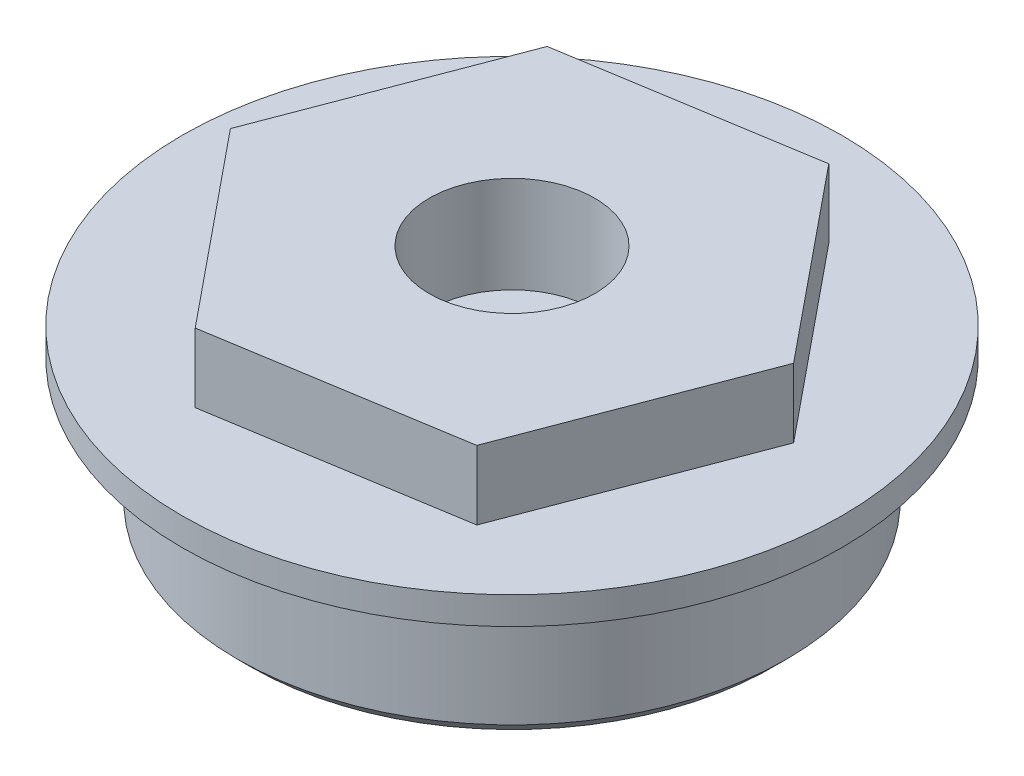
SolidWorks part; units mm, degrees
material "ABS"
ref_plane "Plan de face" through (0, 0, 0) normal (0, 0, 1) x (1, 0, 0)
ref_plane "Plan de dessus" through (0, 0, 0) normal (0, 1, 0) x (1, 0, 0)
ref_plane "Plan de droite" through (0, 0, 0) normal (1, 0, 0) x (0, 0, -1)
sketch "Esquisse1" plane through (0, 0, 0) normal (0, 1, 0) x (1, 0, 0)
  circle A0 centre (0, 0) radius 9.95
  dimension "D1" = 19.9
extrude "Boss.-Extru.1" add sketch "Esquisse1" along normal blind 6
sketch "Esquisse2" plane through (0, 6, 0) normal (0, 1, 0) x (1, 0, 0)
  line L1 (-3.1627, -8.3191) -> (5.6232, -6.8986)
  line L2 (5.6232, -6.8986) -> (8.7859, 1.4205)
  line L3 (8.7859, 1.4205) -> (3.1627, 8.3191)
  line L4 (3.1627, 8.3191) -> (-5.6232, 6.8986)
  line L5 (-5.6232, 6.8986) -> (-8.7859, -1.4205)
  line L6 (-8.7859, -1.4205) -> (-3.1627, -8.3191)
  circle A0 centre (0, 0) radius 7.7076 construction
  circle A1 centre (0, 0) radius 8.9 construction
  dimension "D1" = 17.8
extrude "Boss.-Extru.2" add sketch "Esquisse2" along normal blind 2.5
sketch "Esquisse3" plane through (0, 6, 0) normal (0, 1, 0) x (1, 0, 0)
  circle A0 centre (0, 0) radius 9.95 construction
  circle A1 centre (0, 0) radius 9.95
  circle A2 centre (0, 0) radius 11.95
  dimension "D1" = 2
extrude "Boss.-Extru.3" add sketch "Esquisse3" against normal blind 1
sketch "Esquisse4" plane through (0, 0, 0) normal (0, -1, 0) x (1, 0, 0)
  line L0 (0, 0) -> (0, 9.95) construction
  circle A0 centre (0, 0) radius 9.95 construction
  circle A1 centre (0, 6) radius 1.5
  circle A2 centre (6, 0) radius 1.5
  circle A3 centre (0, -6) radius 1.5
  circle A4 centre (-6, 0) radius 1.5
  point P17 (0, 0)
  dimension "D1" = 3
  dimension "D2" = 6
  dimension "D3" = 4
extrude "Enlèv. mat.-Extru.1" cut sketch "Esquisse4" against normal blind 5
sketch "Esquisse5" plane through (0, 0, 0) normal (0, -1, 0) x (1, 0, 0)
  circle A0 centre (0, 0) radius 1.75
  dimension "D1" = 3.5
extrude "Enlèv. mat.-Extru.2" cut sketch "Esquisse5" against normal through all
sketch "Esquisse6" plane through (0, 8.5, 0) normal (0, 1, 0) x (1, 0, 0)
  circle A0 centre (0, 0) radius 3
  dimension "D1" = 6
extrude "Enlèv. mat.-Extru.3" cut sketch "Esquisse6" against normal blind 3.5
chamfer "Chanfrein1" distance 0.5 angle 45 1 edges at (0, 0, 9.95)
